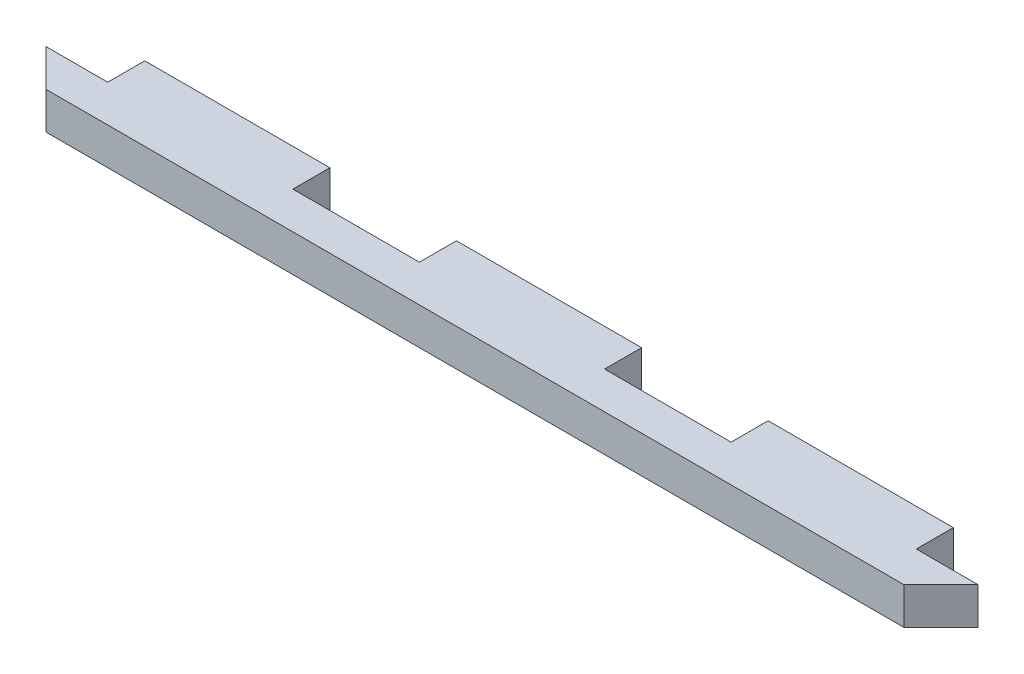
SolidWorks part; units mm, degrees
ref_plane "Front Plane" through (0, 0, 0) normal (0, 0, 1) x (1, 0, 0)
ref_plane "Top Plane" through (0, 0, 0) normal (0, 1, 0) x (1, 0, 0)
ref_plane "Right Plane" through (0, 0, 0) normal (1, 0, 0) x (0, 0, -1)
sketch "Sketch1" plane through (0, 0, 0) normal (0, 1, 0) x (1, 0, 0)
  line L0 (-75.5, 3) -> (0, -72.5)
  line L1 (-75.5, 3) -> (75.5, 3)
  line L2 (-75.5, 3) -> (-75.5, -3)
  line L3 (-75.5, -3) -> (75.5, -3)
  line L4 (75.5, 3) -> (75.5, -3)
  line L5 (-75.5, 3) -> (75.5, -3) construction
  line L6 (-75.5, -3) -> (75.5, 3) construction
  line L7 (0, -72.5) -> (75.5, 3)
  line L8 (0, -72.5) -> (0, -3) construction
  point P0 (0, 0)
  dimension "D1" = 6
  dimension "D2" = 151
sketch "Sketch2" plane through (0, 0, 0) normal (0, 0, 1) x (1, 0, 0)
  line L0 (0, 0) -> (0, 6) construction
  line L1 (-75.5, 0) -> (75.5, 0) construction
  point P4 (0, 3)
  dimension "D1" = 6
extrude "Boss-Extrude1" add sketch "Sketch1" along normal up to vertex (6 mm away) contours L3 L7 L1 L0
sketch "Sketch3" plane through (0, 0, 0) normal (0, -1, 0) x (1, 0, 0)
  line L1 (65.5, -3) -> (35.5, -3)
  line L2 (65.5, -3) -> (65.5, -9)
  line L3 (65.5, -9) -> (35.5, -9)
  line L4 (35.5, -3) -> (35.5, -9)
  line L6 (-65.5, -3) -> (-35.5, -3)
  line L7 (-65.5, -3) -> (-65.5, -9)
  line L8 (-65.5, -9) -> (-35.5, -9)
  line L9 (-35.5, -3) -> (-35.5, -9)
  line L10 (-75.5, -3) -> (75.5, -3) construction
  line L11 (15, -3) -> (-15, -3)
  line L12 (15, -3) -> (15, -9)
  line L13 (15, -9) -> (-15, -9)
  line L14 (-15, -3) -> (-15, -9)
  line L16 (0, -3) -> (0, 0) construction
  line L17 (-65.5, -3) -> (-75.5, -3)
  line L18 (65.5, -3) -> (75.5, -3)
  point P4 (15, -237.8658)
  line M7 (-75.5, -3) -> (75.5, -3)
  dimension "D1" = 30
  dimension "D2" = 10
  dimension "D3" = 6
extrude "Boss-Extrude2" add sketch "Sketch3" against normal up to surface (6 mm away) contours L4 L3 L2 M7 | L14 L13 L12 L11 M7 | L9 L7 L8 M7 up to face at (0, 6, 0)
equation "\"glass_width\"= 181"
equation "\"glass_height\"= 151"
equation "\"glass_thickness\"= 2.5"
equation "\"brood_space\"= 42"
equation "\"t1\"= 6"
equation "\"t2\"= 6"
equation "\"box_depth\"= \"brood_space\" + \"glass_thickness\" + \"glass_thickness\" + \"t2\" + \"t2\""
equation "\"box_width\"= \"glass_width\" + \"t1\" + \"t1\""
equation "\"food_height\"= 70"
equation "\"box_height\"= \"glass_height\" + ( \"t1\" * 3 ) + \"food_height\""
equation "\"D2@Sketch1\"=\"glass_width\"-30"
equation "\"D1@Sketch2\"=\"t2\""
equation "\"entry_height\"= 24"
equation "\"entry_diameter\"= 8"
equation "\"food_top_clearance\"= 10"
equation "\"bar_width\"= 20"
equation "\"glassblocker_lower_height\"= 10"
equation "\"lower_edge_stickout\"=6"
equation "\"D3@Sketch3\"=\"t1\""
